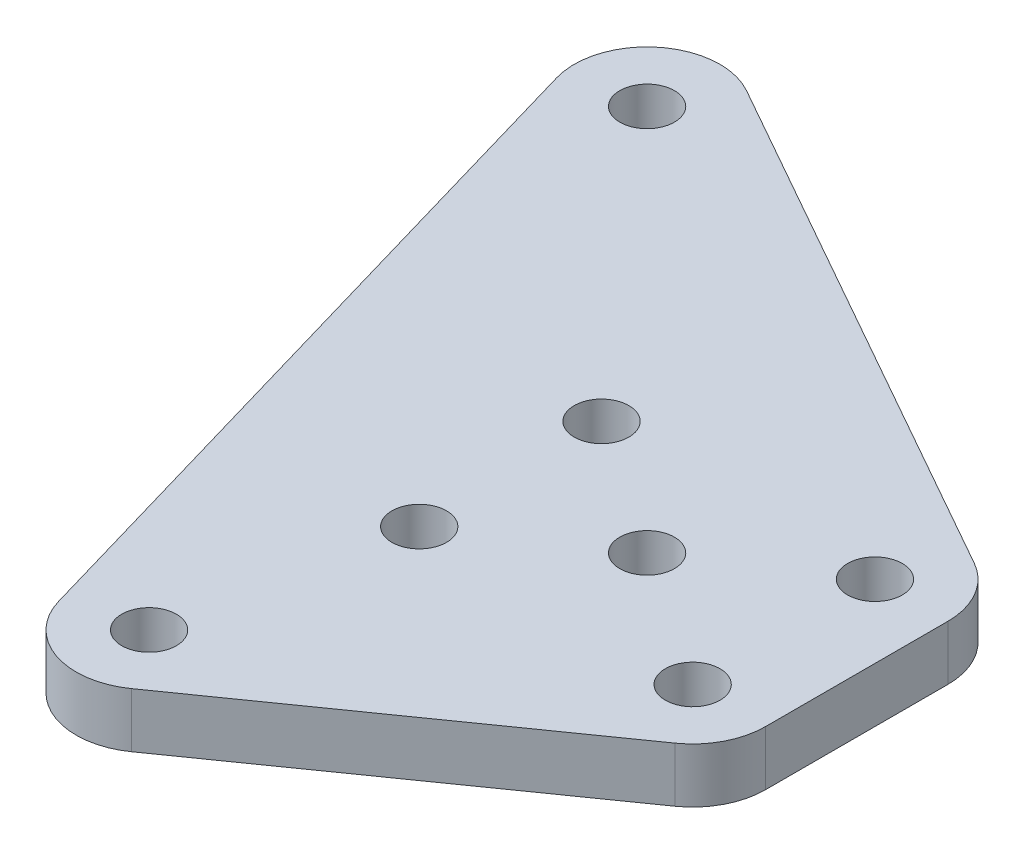
SolidWorks part; units mm, degrees
ref_plane "Front Plane" through (0, 0, 0) normal (0, 0, 1) x (1, 0, 0)
ref_plane "Top Plane" through (0, 0, 0) normal (0, 1, 0) x (1, 0, 0)
ref_plane "Right Plane" through (0, 0, 0) normal (1, 0, 0) x (0, 0, -1)
sketch "Sketch1" plane through (0, 0, 0) normal (0, 1, 0) x (1, 0, 0)
  line L4 (-0.8407, -22.5376) -> (16.6593, -10.2171)
  line L5 (18.3566, -6.9463) -> (18.3566, 3.0537)
  line L6 (16.3234, 6.5367) -> (-12.3898, 22.7499)
  line L7 (-18.1973, 18.1492) -> (-6.9841, -20.3845)
  arc A6 (16.6593, -10.2171) -> (18.3566, -6.9463) centre (14.3566, -6.9463) ccw
  arc A7 (18.3566, 3.0537) -> (16.3234, 6.5367) centre (14.3566, 3.0537) ccw
  arc A8 (-12.3898, 22.7499) -> (-18.1973, 18.1492) centre (-14.3566, 19.2669) ccw
  arc A9 (-6.9841, -20.3845) -> (-0.8407, -22.5376) centre (-3.1434, -19.2669) ccw
  circle A10 centre (14.3566, -6.9463) radius 1.5
  circle A11 centre (14.3566, 3.0537) radius 1.5
  circle A12 centre (6.8566, -1.9463) radius 1.5
  circle A13 centre (-3.1434, -19.2669) radius 1.5
  circle A14 centre (-0.6434, -6.9463) radius 1.5
  circle A15 centre (-0.6434, 3.0537) radius 1.5
  circle A16 centre (-14.3566, 19.2669) radius 1.5
extrude "Boss-Extrude1" add sketch "Sketch1" along normal blind 3
